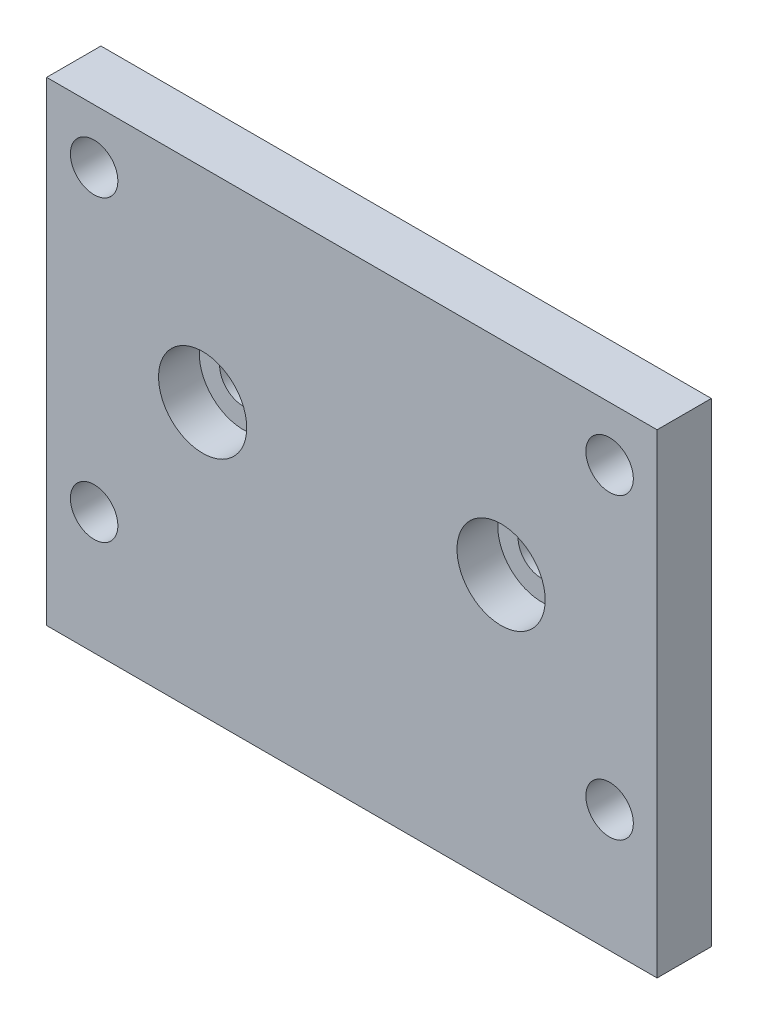
SolidWorks part; units mm, degrees
ref_plane "正面" through (0, 0, 0) normal (0, 0, 1) x (1, 0, 0)
ref_plane "平面" through (0, 0, 0) normal (0, 1, 0) x (1, 0, 0)
ref_plane "右側面" through (0, 0, 0) normal (1, 0, 0) x (0, 0, -1)
sketch "ｽｹｯﾁ1" plane through (0, 0, 0) normal (0, 0, 1) x (1, 0, 0)
  line L1 (22.5, -17.5) -> (-22.5, -17.5)
  line L2 (22.5, -17.5) -> (22.5, 17.5)
  line L3 (22.5, 17.5) -> (-22.5, 17.5)
  line L4 (-22.5, -17.5) -> (-22.5, 17.5)
  line L5 (22.5, -17.5) -> (-22.5, 17.5) construction
  line L6 (22.5, 17.5) -> (-22.5, -17.5) construction
  point P0 (0, 0)
  dimension "D1" = 35
  dimension "D2" = 45
extrude "ﾎﾞｽ - 押し出し1" add sketch "ｽｹｯﾁ1" along normal blind 4
sketch "ｽｹｯﾁ2" plane through (0, 0, 4) normal (0, 0, 1) x (1, 0, 0)
  line L0 (0, -17.5) -> (0, 17.5)
  line L1 (-22.5, -17.5) -> (22.5, -17.5) construction
  line L2 (22.5, 17.5) -> (-22.5, 17.5) construction
  line L3 (22.5, 0) -> (-22.5, 0)
  line L4 (22.5, -17.5) -> (22.5, 17.5) construction
  line L5 (-22.5, 17.5) -> (-22.5, -17.5) construction
  circle A0 centre (-19, 13.5) radius 1.75
  circle A1 centre (19, 13.5) radius 1.75
  circle A2 centre (-19, -8.5) radius 1.75
  circle A3 centre (19, -8.5) radius 1.75
  circle A4 centre (-11, 2.5) radius 1.75
  circle A5 centre (11, 2.5) radius 1.75
  dimension "D1" = 3.5
  dimension "D2" = 3.5
  dimension "D4" = 3.5
  dimension "D5" = 3.5
  dimension "D13" = 3.5
  dimension "D15" = 3.5
  dimension "D3" = 38
  dimension "D6" = 22
  dimension "D7" = 22
  dimension "D8" = 38
  dimension "D9" = 4
  dimension "D10" = 19
  dimension "D11" = 19
  dimension "D12" = 4
  dimension "D14" = 11
  dimension "D16" = 22
  dimension "D17" = 11
extrude "ｶｯﾄ - 押し出し1" cut sketch "ｽｹｯﾁ2" against normal through all contours A0 | A2 | A1 | A3 | A4 | A5
sketch "ｽｹｯﾁ3" plane through (0, 0, 4) normal (0, 0, 1) x (1, 0, 0)
  circle A0 centre (-11, 2.5) radius 3.25
  circle A1 centre (11, 2.5) radius 3.25
  dimension "D1" = 6.5
  dimension "D2" = 6.5
extrude "ｶｯﾄ - 押し出し2" cut sketch "ｽｹｯﾁ3" against normal blind 3
